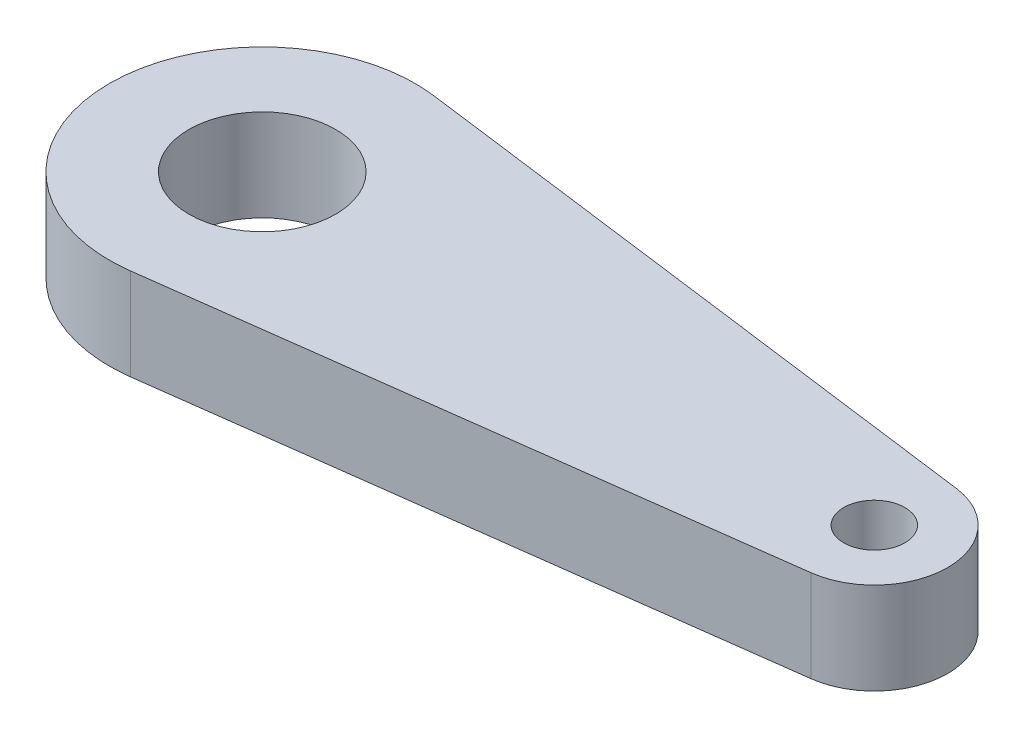
SolidWorks part; units mm, degrees
ref_plane "Front Plane" through (0, 0, 0) normal (0, 0, 1) x (1, 0, 0)
ref_plane "Top Plane" through (0, 0, 0) normal (0, 1, 0) x (1, 0, 0)
ref_plane "Right Plane" through (0, 0, 0) normal (1, 0, 0) x (0, 0, -1)
sketch "Sketch2" plane through (0, 0, 0) normal (0, 1, 0) x (1, 0, 0)
  line L0 (-36.4106, 0) -> (32.0894, 0) construction
  line L1 (-22.2856, 12.3939) -> (26.8694, 5.9491)
  line L2 (-22.2856, -12.3939) -> (26.8694, -5.9491)
  circle A0 centre (26.0894, 0) radius 2.5
  arc A1 (26.8694, -5.9491) -> (26.8694, 5.9491) centre (26.0894, 0) ccw
  arc A2 (-22.2856, 12.3939) -> (-22.2856, -12.3939) centre (-23.9106, 0) ccw
  circle A3 centre (-23.9106, 0) radius 6
  dimension "D1" = 12
  dimension "D2" = 5
  dimension "D3" = 25
  dimension "D5" = 12
  dimension "D4" = 50
extrude "Boss-Extrude1" add sketch "Sketch2" along normal blind 7.5
sketch "Sketch3" plane through (0, 7.5, 0) normal (0, 1, 0) x (1, 0, 0)
  line L0 (-17.9106, 0) -> (23.5894, 0) construction
  circle A0 centre (-23.9106, 0) radius 6 construction
  circle A1 centre (26.0894, 0) radius 2.5 construction
